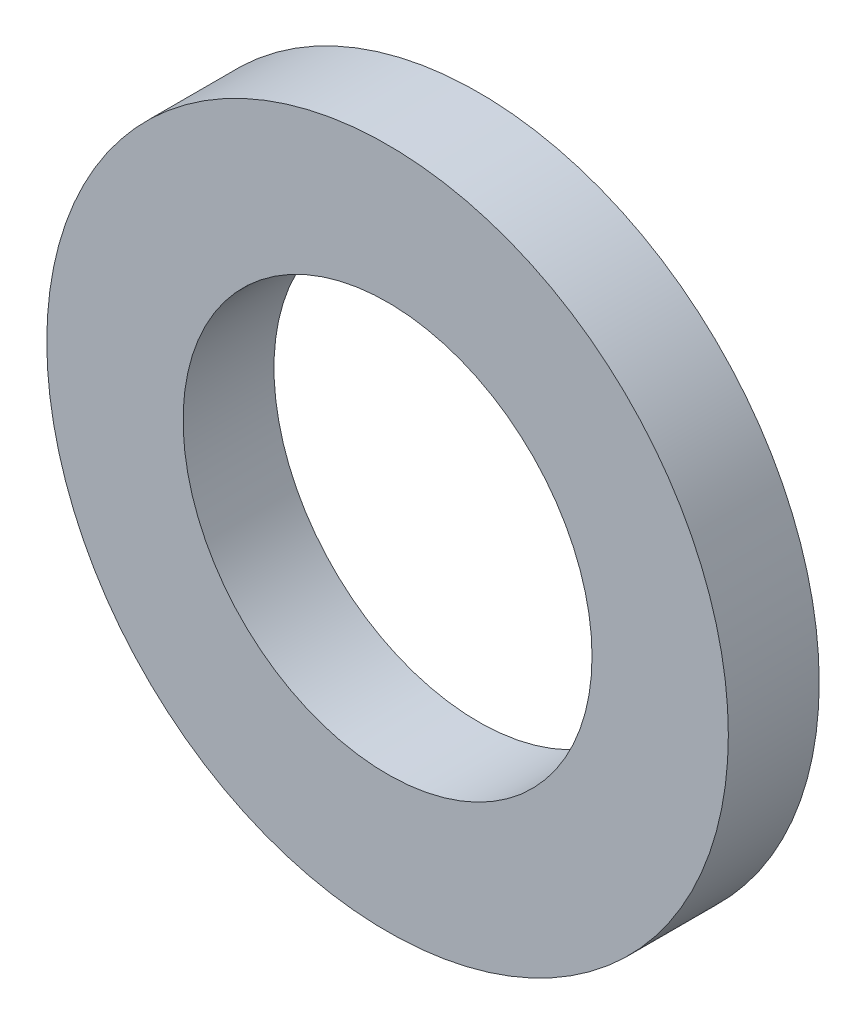
SolidWorks part; units mm, degrees
ref_plane "前基準面" through (0, 0, 0) normal (0, 0, 1) x (1, 0, 0)
ref_plane "上基準面" through (0, 0, 0) normal (0, 1, 0) x (1, 0, 0)
ref_plane "右基準面" through (0, 0, 0) normal (1, 0, 0) x (0, 0, -1)
sketch "草圖1" plane through (0, 0, 0) normal (0, 0, 1) x (1, 0, 0)
  circle A0 centre (0, 0) radius 4.5
  circle A1 centre (0, 0) radius 7.5
  dimension "D1" = 9
  dimension "D2" = 3
extrude "填料-伸長1" add sketch "草圖1" along normal blind 2
